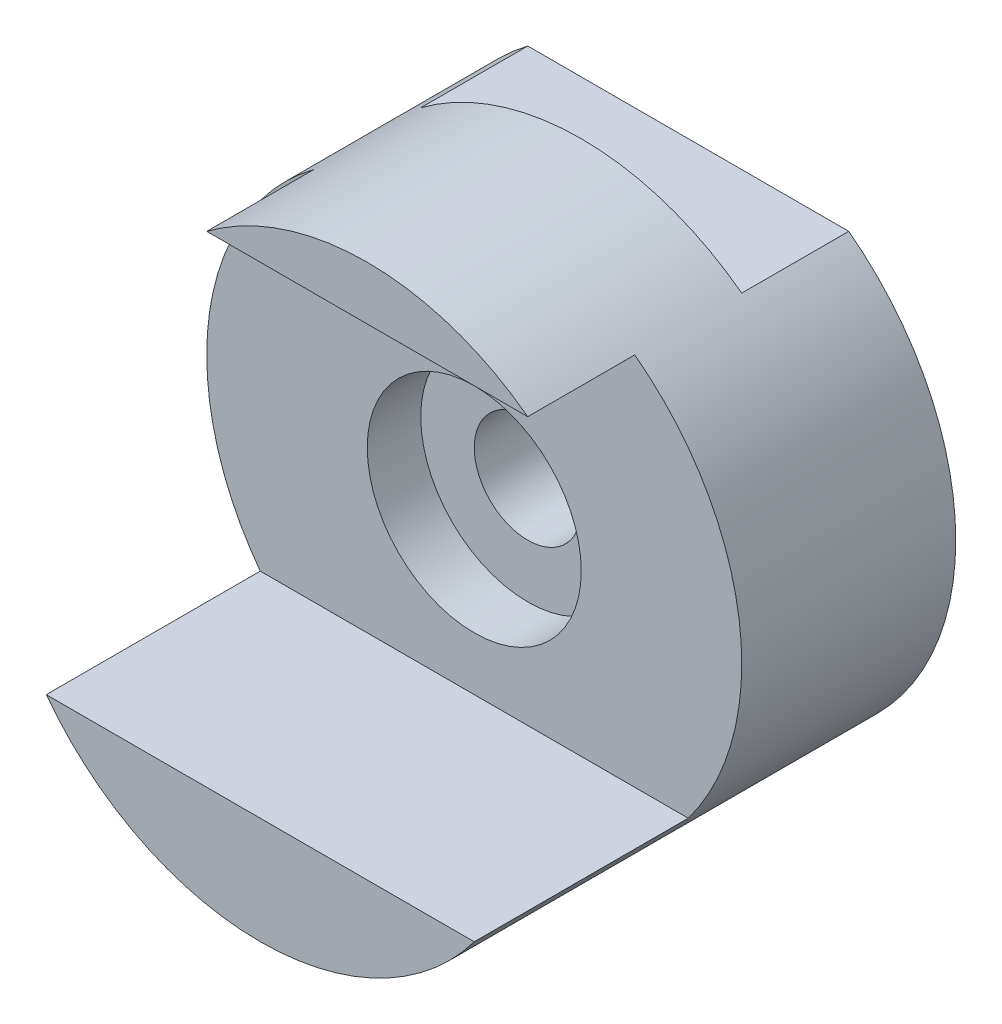
SolidWorks part; units mm, degrees
ref_plane "Front" through (0, 0, 0) normal (0, 0, 1) x (1, 0, 0)
ref_plane "Top" through (0, 0, 0) normal (0, 1, 0) x (1, 0, 0)
ref_plane "Right" through (0, 0, 0) normal (1, 0, 0) x (0, 0, -1)
sketch "Sketch1" plane through (0, 0, 0) normal (0, 0, 1) x (1, 0, 0)
  circle A0 centre (0, 0) radius 5
  circle A1 centre (0, 0) radius 1
  dimension "D1" = 2
  dimension "D2" = 10
extrude "Boss-Extrude1" add sketch "Sketch1" along normal blind 8
sketch "Sketch2" plane through (0, 0, 0) normal (1, 0, 0) x (0, 0, -1)
  line L0 (-8, -3) -> (-4, -3)
  line L1 (-8, 5) -> (-8, -5) construction
  line L2 (-4, -3) -> (-4, 4)
  line L3 (-4, 4) -> (-6, 4)
  line L4 (-6, 4) -> (-6, 5)
  line L5 (0, 5) -> (-8, 5) construction
  line L6 (-6, 5) -> (-8, 5)
  line L7 (-8, 5) -> (-8, -3)
  line L8 (0, -5) -> (0, 5) construction
  line L9 (0, 5) -> (-2, 5)
  line L10 (0, 5) -> (0, 4)
  line L11 (0, 4) -> (-2, 4)
  line L12 (-2, 5) -> (-2, 4)
  dimension "D1" = 2
  dimension "D2" = 2
  dimension "D3" = 1
  dimension "D4" = 7
  dimension "D5" = 2
  dimension "D6" = 1
  dimension "D7" = 0
extrude "Cut-Extrude1" cut sketch "Sketch2" against normal mid plane 18
sketch "Sketch3" plane through (0, 0, 4) normal (0, 0, 1) x (1, 0, 0)
  circle A0 centre (0, 0) radius 2
  dimension "D1" = 4
extrude "Cut-Extrude2" cut sketch "Sketch3" against normal blind 1
